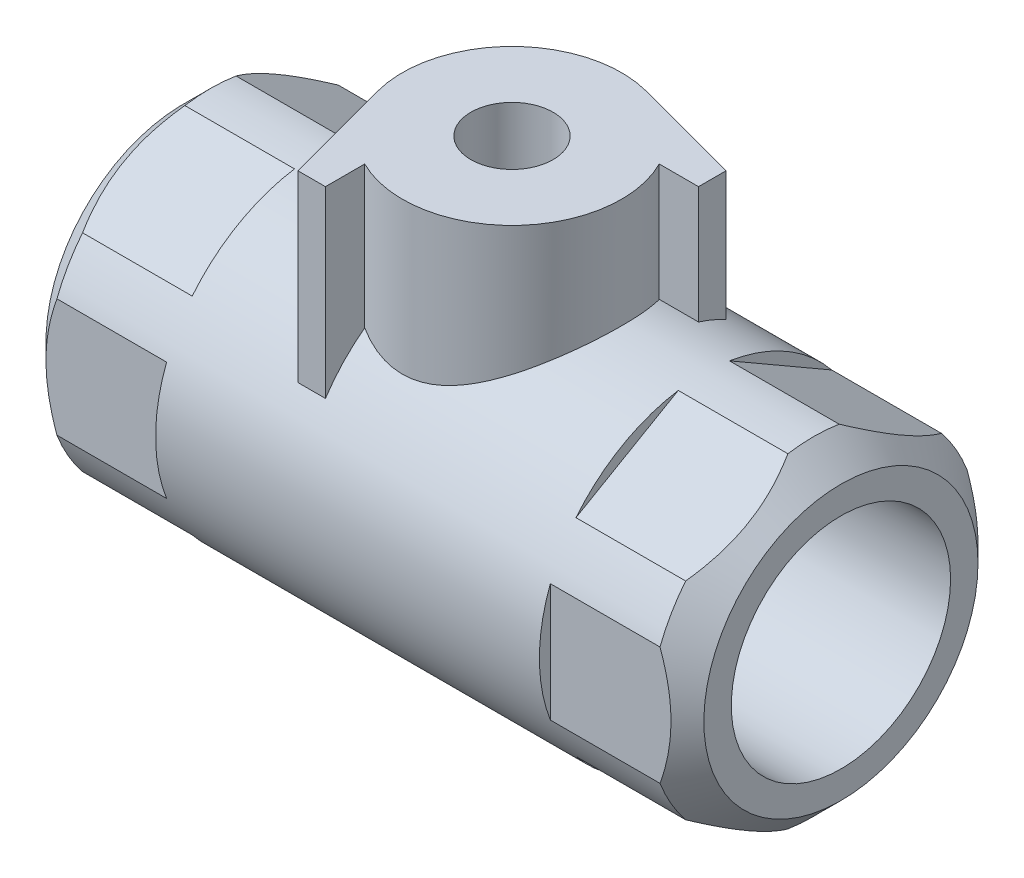
SolidWorks part; units mm, degrees
material "Alloy Steel"
ref_plane "Front Plane" through (0, 0, 0) normal (0, 0, 1) x (1, 0, 0)
ref_plane "Top Plane" through (0, 0, 0) normal (0, 1, 0) x (1, 0, 0)
ref_plane "Right Plane" through (0, 0, 0) normal (1, 0, 0) x (0, 0, -1)
sketch "Sketch1" plane through (0, 0, 0) normal (1, 0, 0) x (0, 0, -1)
  circle A0 centre (0, 0) radius 30
  dimension "D1" = 60
extrude "Boss-Extrude1" add sketch "Sketch1" along normal mid plane 120
chamfer "Chamfer1" distance 5 angle 45 2 edges at (-60, 0, -30) (60, 0, -30)
sketch "Sketch2" plane through (60, 0, 0) normal (1, 0, 0) x (0, 0, -1)
  line L0 (-36.9741, 0) -> (36.9741, 0) construction
  line L1 (28, 10.7703) -> (28, -10.7703)
  arc A0 (28, -10.7703) -> (28, 10.7703) centre (0, 0) ccw
  circle A1 centre (0, 0) radius 30 construction
  point P5 (0, 0)
  dimension "D1" = 28
extrude "Cut-Extrude1" cut sketch "Sketch2" against normal blind 25
pattern_circular "CirPattern1" count 6 over 360 about axis through (0, 0, 0) along (1, 0, 0) of "Cut-Extrude1"
sketch "Sketch3" plane through (60, 0, 0) normal (1, 0, 0) x (0, 0, -1)
  circle A0 centre (0, 0) radius 20
  dimension "D1" = 40
extrude "Cut-Extrude2" cut sketch "Sketch3" against normal blind 30
sketch "Sketch5" plane through (30, 0, 0) normal (1, 0, 0) x (0, 0, -1)
  circle A0 centre (0, 0) radius 12.5
  dimension "D1" = 25
extrude "Cut-Extrude3" cut sketch "Sketch5" against normal through all
sketch "Sketch4" plane through (0, 0, 0) normal (0, 0, 1) x (1, 0, 0)
  line L0 (0, 40.5499) -> (0, -40.5499) construction
  line L1 (0, 17) -> (0, -17)
  arc A0 (0, -17) -> (0, 17) centre (0, 0) ccw
  point P4 (0, 0)
  dimension "D1" = 17
revolve "Cut-Revolve1" cut sketch "Sketch4" angle 360 about L0
chamfer "Chamfer2" distance 5 angle 45 1 edges at (30, 0, -12.5)
mirror "Mirror1" about plane through (0, 0, 0) normal (1, 0, 0) of "Cut-Extrude1", "CirPattern1", "Cut-Extrude2", "Chamfer2"
ref_plane "Plane1" through (0, 50, 0) normal (0, 1, 0) x (1, 0, 0)
sketch "Sketch6" plane through (0, 50, 0) normal (0, 1, 0) x (1, 0, 0)
  line L0 (17.8606, 9) -> (25.0254, 9)
  line L1 (25.0254, 9) -> (25.0254, 14)
  line L2 (25.0254, 14) -> (5.1764, 19.3185)
  line L3 (-33.2286, 0) -> (33.2286, 0) construction
  line L4 (-19.505, 19.505) -> (19.505, -19.505) construction
  line L5 (-14, -25.0254) -> (-19.3185, -5.1764)
  line L6 (-9, -25.0254) -> (-14, -25.0254)
  line L7 (-9, -17.8606) -> (-9, -25.0254)
  arc A0 (5.1764, 19.3185) -> (-19.3185, -5.1764) centre (0, 0) ccw
  arc A1 (-9, -17.8606) -> (17.8606, 9) centre (0, 0) ccw
  point P12 (0, 0)
  dimension "D1" = 135
  dimension "D4" = 40
  dimension "D2" = 14
  dimension "D3" = 75
  dimension "D5" = 5
extrude "Boss-Extrude2" add sketch "Sketch6" against normal up to surface (33.4552 mm away)
sketch "Sketch8" plane through (0, 50, 0) normal (0, 1, 0) x (1, 0, 0)
  circle A0 centre (0, 0) radius 7.5
  dimension "D1" = 15
extrude "Cut-Extrude4" cut sketch "Sketch8" against normal up to next
